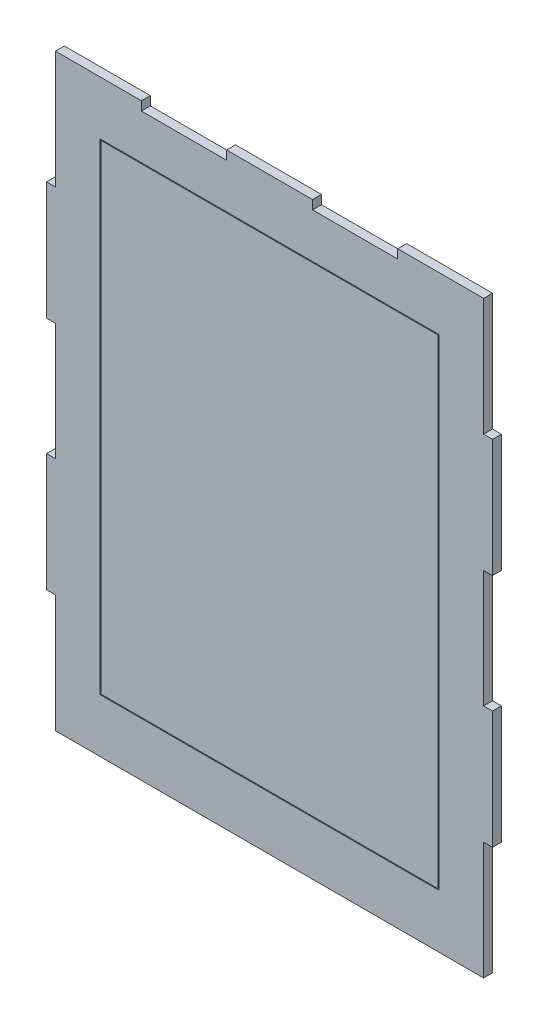
SolidWorks part; units mm, degrees
material "Contreplaqué pin"
ref_plane "Plan de face" through (0, 0, 0) normal (0, 0, 1) x (1, 0, 0)
ref_plane "Plan de dessus" through (0, 0, 0) normal (0, 1, 0) x (1, 0, 0)
ref_plane "Plan de droite" through (0, 0, 0) normal (1, 0, 0) x (0, 0, -1)
sketch "Esquisse1" plane through (0, 0, 0) normal (0, 0, 1) x (1, 0, 0)
  line L0 (0, 66) -> (5, 66) construction
  line L1 (5, 0) -> (245, 0) construction
  line L2 (0, 66) -> (0, 132) construction
  line L3 (5, 330) -> (53, 330) construction
  line L4 (250, 66) -> (250, 132) construction
  line L5 (5, 66) -> (5, 0) construction
  line L6 (0, 132) -> (5, 132) construction
  line L7 (5, 132) -> (5, 198) construction
  line L8 (5, 198) -> (0, 198) construction
  line L9 (5, 330) -> (5, 264) construction
  line L10 (5, 264) -> (0, 264) construction
  line L11 (0, 198) -> (0, 264) construction
  line L12 (250, 264) -> (245, 264) construction
  line L13 (245, 264) -> (245, 330) construction
  line L14 (250, 198) -> (245, 198) construction
  line L15 (245, 198) -> (245, 132) construction
  line L16 (245, 132) -> (250, 132) construction
  line L17 (250, 66) -> (245, 66) construction
  line L18 (245, 66) -> (245, 0) construction
  line L19 (250, 198) -> (250, 264) construction
  line L20 (53, 330) -> (53, 325) construction
  line L21 (53, 325) -> (101, 325) construction
  line L22 (101, 325) -> (101, 330) construction
  line L23 (149, 330) -> (149, 325) construction
  line L24 (149, 325) -> (197, 325) construction
  line L25 (197, 325) -> (197, 330) construction
  line L26 (101, 330) -> (149, 330) construction
  line L27 (197, 330) -> (245, 330) construction
  line L28 (30, 300) -> (220, 300)
  line L29 (220, 300) -> (220, 30)
  line L30 (220, 30) -> (30, 30)
  line L31 (30, 30) -> (30, 300)
  line L32 (30.5, 299.5) -> (219.5, 299.5)
  line L33 (219.5, 299.5) -> (219.5, 30.5)
  line L34 (219.5, 30.5) -> (30.5, 30.5)
  line L35 (30.5, 30.5) -> (30.5, 299.5)
  line L36 (196.9, 330.1) -> (245.1, 330.1)
  line L37 (245.1, 264.1) -> (245.1, 330.1)
  line L38 (250.1, 264.1) -> (245.1, 264.1)
  line L39 (250.1, 197.9) -> (250.1, 264.1)
  line L40 (250.1, 197.9) -> (245.1, 197.9)
  line L41 (245.1, 197.9) -> (245.1, 132.1)
  line L42 (245.1, 132.1) -> (250.1, 132.1)
  line L43 (250.1, 65.9) -> (250.1, 132.1)
  line L44 (250.1, 65.9) -> (245.1, 65.9)
  line L45 (245.1, 65.9) -> (245.1, -0.1)
  line L46 (4.9, -0.1) -> (245.1, -0.1)
  line L47 (4.9, 65.9) -> (4.9, -0.1)
  line L48 (-0.1, 65.9) -> (4.9, 65.9)
  line L49 (-0.1, 65.9) -> (-0.1, 132.1)
  line L50 (-0.1, 132.1) -> (4.9, 132.1)
  line L51 (4.9, 132.1) -> (4.9, 197.9)
  line L52 (4.9, 197.9) -> (-0.1, 197.9)
  line L53 (-0.1, 197.9) -> (-0.1, 264.1)
  line L54 (4.9, 264.1) -> (-0.1, 264.1)
  line L55 (4.9, 330.1) -> (4.9, 264.1)
  line L56 (4.9, 330.1) -> (53.1, 330.1)
  line L57 (53.1, 330.1) -> (53.1, 325.1)
  line L58 (53.1, 325.1) -> (100.9, 325.1)
  line L59 (100.9, 325.1) -> (100.9, 330.1)
  line L60 (100.9, 330.1) -> (149.1, 330.1)
  line L61 (149.1, 330.1) -> (149.1, 325.1)
  line L62 (149.1, 325.1) -> (196.9, 325.1)
  line L63 (196.9, 325.1) -> (196.9, 330.1)
  dimension "D1" = 250
  dimension "D2" = 330
  dimension "D3" = 5
  dimension "D4" = 5
  dimension "D5" = 5
  dimension "D6" = 30
  dimension "D7" = 30
  dimension "D8" = 30
  dimension "D9" = 30
  dimension "D10" = 0.5
  dimension "D11" = 0.1
extrude "Boss.-Extru.1" add sketch "Esquisse1" along normal blind 5 contours L35 L34 L33 L32 | L63 L62 L61 L60 L59 L58 L57 L56 L55 L54 L53 L52 L51 L50 L49 L48 L47 L46 L45 L44 L43 L42 L41 L40 L39 L38 L37 L36 L30 L31 L28 L29
hole_wizard "Diamètre du perçage Ø5.0 (5)1" positions "Esquisse2" profile "Esquisse3" hole size "Ø5.0" standard "DIN"
sketch "Esquisse2" plane through (0, 0, 5) normal (0, 0, 1) x (1, 0, 0)
  line L0 (35, 295) -> (35, 100) construction
  line L1 (35, 100) -> (215, 100) construction
  line L2 (215, 100) -> (215, 295) construction
  line L3 (215, 295) -> (35, 295) construction
  line L5 (5, 198) -> (5, 132) construction
  line L6 (101, 325) -> (53, 325) construction
  line L7 (245, 132) -> (245, 198) construction
  line L8 (5, 0) -> (245, 0) construction
  point P0 (35, 295)
  point P2 (215, 295)
  point P4 (215, 100)
  point P6 (35, 100)
  dimension "D1" = 30
  dimension "D2" = 30
  dimension "D3" = 30
  dimension "D4" = 100
sketch "Esquisse3" plane through (35, 295, 5) normal (1, 0, 0) x (0, -1, 0)
  line L0 (0, 0) -> (0, 5)
  line L1 (0, 5) -> (2.5, 5)
  line L2 (2.5, 5) -> (2.5, 0)
  line L5 (2.5, 0) -> (0, 0)
  line L11 (0, -6.35) -> (0, 107.95) construction
  dimension "Diamètre du perçage jusqu'au prochain" = 5
  dimension "Profondeur du perçage jusqu'au prochain" = 5
